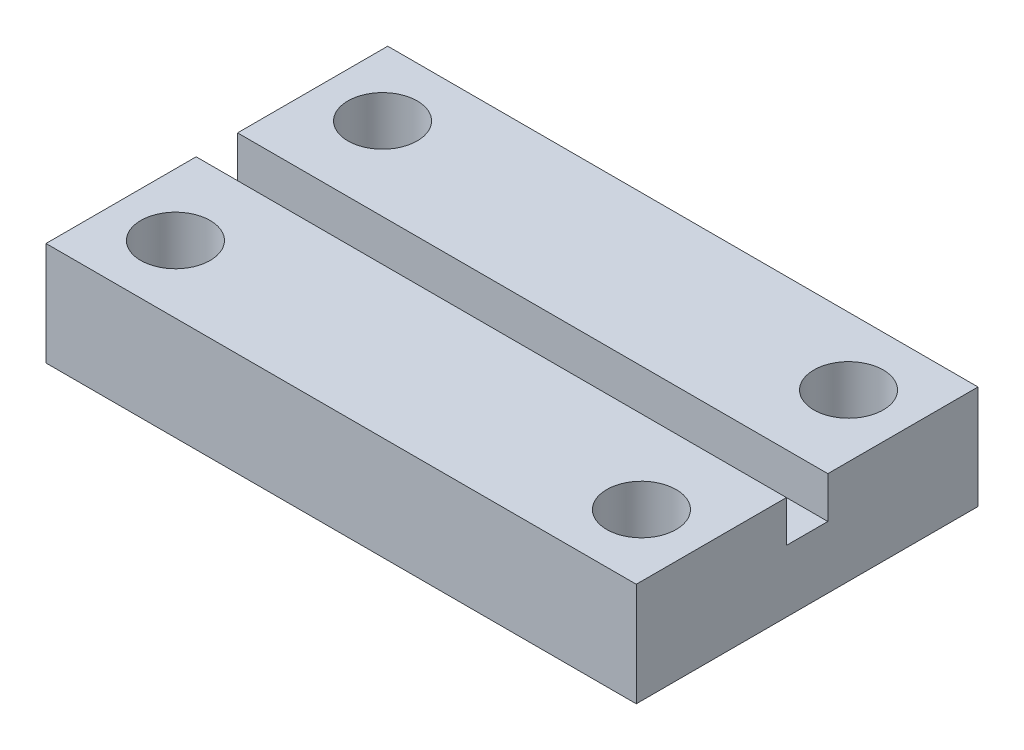
SolidWorks part; units mm, degrees
ref_plane "Front Plane" through (0, 0, 0) normal (0, 0, 1) x (1, 0, 0)
ref_plane "Top Plane" through (0, 0, 0) normal (0, 1, 0) x (1, 0, 0)
ref_plane "Right Plane" through (0, 0, 0) normal (1, 0, 0) x (0, 0, -1)
sketch "Sketch1" plane through (0, 0, 0) normal (0, 1, 0) x (1, 0, 0)
  line L1 (0, 0) -> (57, 0)
  line L2 (0, 0) -> (0, 33)
  line L3 (0, 33) -> (57, 33)
  line L4 (57, 0) -> (57, 33)
  dimension "D1" = 33
  dimension "D2" = 57
extrude "Boss-Extrude1" add sketch "Sketch1" along normal blind 10
sketch "Sketch3" plane through (0, 0, 0) normal (0, -1, 0) x (1, 0, 0)
  line L2 (0, 0) -> (57, 0) construction
  line L3 (0, -33) -> (0, 0) construction
  circle A0 centre (6, -6.5) radius 3.35
  point P4 (28.5, 0)
  point P9 (0, -16.5)
  dimension "D1" = 22.5
  dimension "D3" = 6.7
  dimension "D2" = 10
extrude "Cut-Extrude1" cut sketch "Sketch3" against normal through all
sketch "Sketch4" plane through (0, 0, 0) normal (0, -1, 0) x (1, 0, 0)
  line L2 (57, 0) -> (57, -33) construction
  line L3 (57, -33) -> (0, -33) construction
  circle A0 centre (51, -26.5) radius 3.35
  point P5 (57, -16.5)
  point P10 (28.5, -33)
  dimension "D1" = 10
  dimension "D3" = 6.7
  dimension "D2" = 22.5
extrude "Cut-Extrude2" cut sketch "Sketch4" against normal through all
ref_plane "Plane1" through (0, 0, 0) normal (1, 0, 0) x (0, 0, -1)
sketch "Sketch10" plane through (0, 0, 0) normal (0, -1, 0) x (1, 0, 0)
  line L2 (57, -33) -> (0, -33) construction
  line L3 (57, 0) -> (57, -33) construction
  circle A0 centre (6, -26.5) radius 3.35
  point P5 (28.5, -33)
  point P8 (57, -16.5)
  dimension "D1" = 22.5
  dimension "D3" = 6.7
  dimension "D2" = 10
extrude "Cut-Extrude5" cut sketch "Sketch10" against normal through all
sketch "Sketch12" plane through (0, 0, 0) normal (0, -1, 0) x (1, 0, 0)
  line L2 (57, 0) -> (57, -33) construction
  line L3 (0, 0) -> (57, 0) construction
  circle A0 centre (51, -6.5) radius 3.35
  point P5 (57, -16.5)
  point P10 (28.5, 0)
  dimension "D3" = 6.7
  dimension "D1" = 10
  dimension "D2" = 22.5
extrude "Cut-Extrude6" cut sketch "Sketch12" against normal through all
sketch "Sketch13" plane through (0, 0, -33) normal (0, 0, -1) x (-1, 0, 0)
  line L0 (-28.5, 10) -> (-28.5, 0) construction
  line L1 (-57, 10) -> (0, 10) construction
  line L2 (-57, 0) -> (0, 0) construction
  line L3 (-57, 5) -> (0, 5) construction
  line L4 (-57, 10) -> (-57, 0) construction
sketch "Sketch16" plane through (0, 10, 0) normal (0, 1, 0) x (1, 0, 0)
  line L0 (0, 33) -> (0, 0) construction
  line L1 (0, 18.5) -> (57, 18.5)
  line L2 (0, 18.5) -> (0, 14.5)
  line L3 (0, 14.5) -> (57, 14.5)
  line L4 (57, 18.5) -> (57, 14.5)
  line L5 (57, 0) -> (57, 33) construction
  point P8 (0, 16.5)
  point P9 (0, 16.5)
  dimension "D1" = 4
  dimension "D2" = 0
extrude "Cut-Extrude7" cut sketch "Sketch16" against normal blind 4
